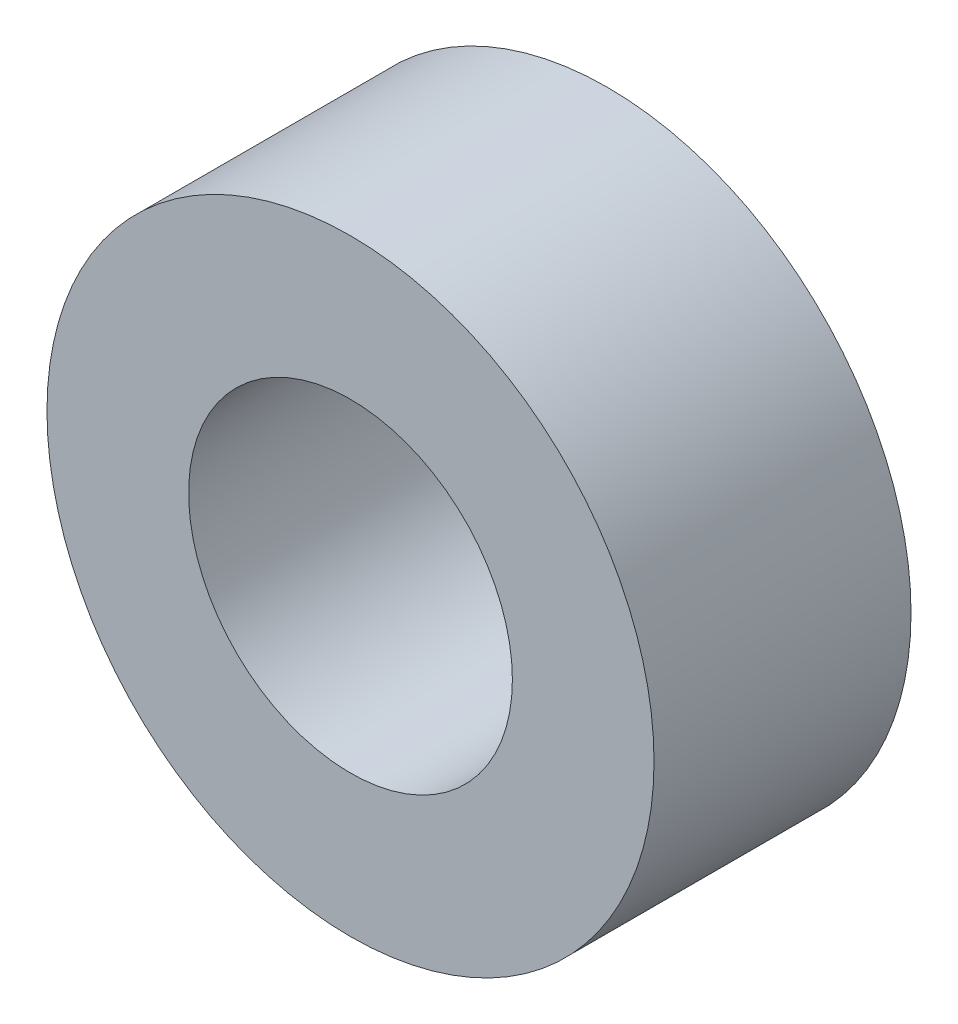
SolidWorks part; units mm, degrees
material "PET"
ref_plane "Front Plane" through (0, 0, 0) normal (0, 0, 1) x (1, 0, 0)
ref_plane "Top Plane" through (0, 0, 0) normal (0, 1, 0) x (1, 0, 0)
ref_plane "Right Plane" through (0, 0, 0) normal (1, 0, 0) x (0, 0, -1)
sketch "Sketch1" plane through (0, 0, 0) normal (0, 0, 1) x (1, 0, 0)
  circle A0 centre (0, 0) radius 2
  circle A1 centre (0, 0) radius 3.75
  dimension "D1" = 4
  dimension "D2" = 7.5
extrude "Boss-Extrude1" add sketch "Sketch1" along normal blind 3.175
